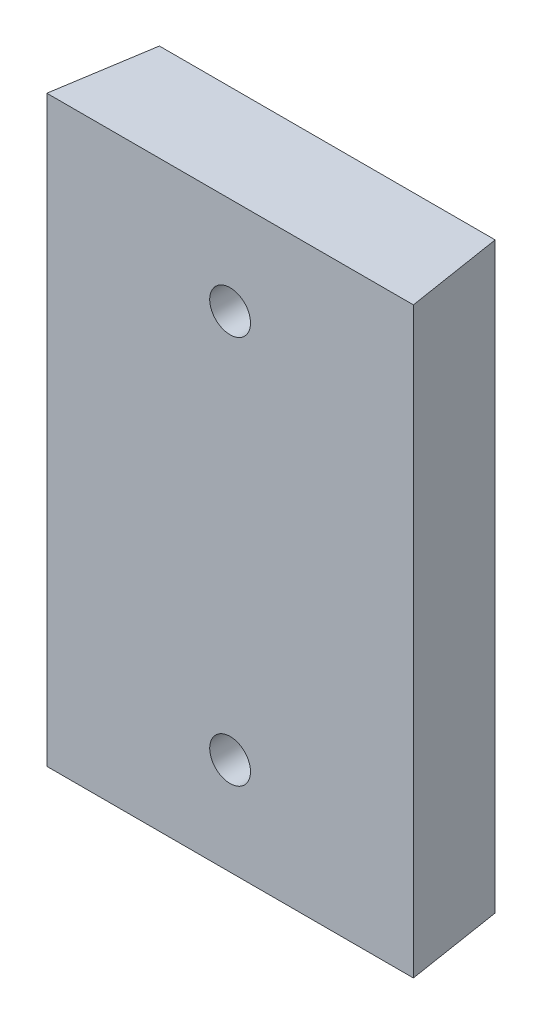
SolidWorks part; units mm, degrees
ref_plane "Ön Düzlem" through (0, 0, 0) normal (0, 0, 1) x (1, 0, 0)
ref_plane "Üst Düzlem" through (0, 0, 0) normal (0, 1, 0) x (1, 0, 0)
ref_plane "Sağ Düzlem" through (0, 0, 0) normal (1, 0, 0) x (0, 0, -1)
sketch "Çizim1" plane through (0, 0, 0) normal (0, 0, 1) x (1, 0, 0)
  line L0 (-21.9008, -30) -> (21.9008, -30)
  line L1 (-21.9008, -30) -> (-21.9008, 30)
  line L2 (-21.9008, 30) -> (21.9008, 30)
  line L3 (21.9008, -30) -> (21.9008, 30)
  circle A0 centre (0, -20) radius 2.1
  circle A1 centre (0, 20) radius 2.1
extrude "Yükseklik-Ekstrüzyon1" add sketch "Çizim1" along normal blind 10
sketch "Çizim2" plane through (0, 30, 0) normal (0, 1, 0) x (1, 0, 0)
  line L0 (-15.609, 10.5479) -> (-27.5179, 10.5479)
  line L1 (-18.9378, -10.4693) -> (-15.609, 10.5479)
  line L2 (-27.5179, 10.5479) -> (-27.5179, -12.1489)
  line L3 (-27.5179, -12.1489) -> (-18.9378, -10.4693)
  line L5 (27.5179, -12.1489) -> (18.9378, -10.4693)
  line L6 (27.5179, 10.5479) -> (27.5179, -12.1489)
  line L7 (18.9378, -10.4693) -> (15.609, 10.5479)
  line L8 (15.609, 10.5479) -> (27.5179, 10.5479)
extrude "Kes-Ekstrüzyon1" cut sketch "Çizim2" against normal blind 81
